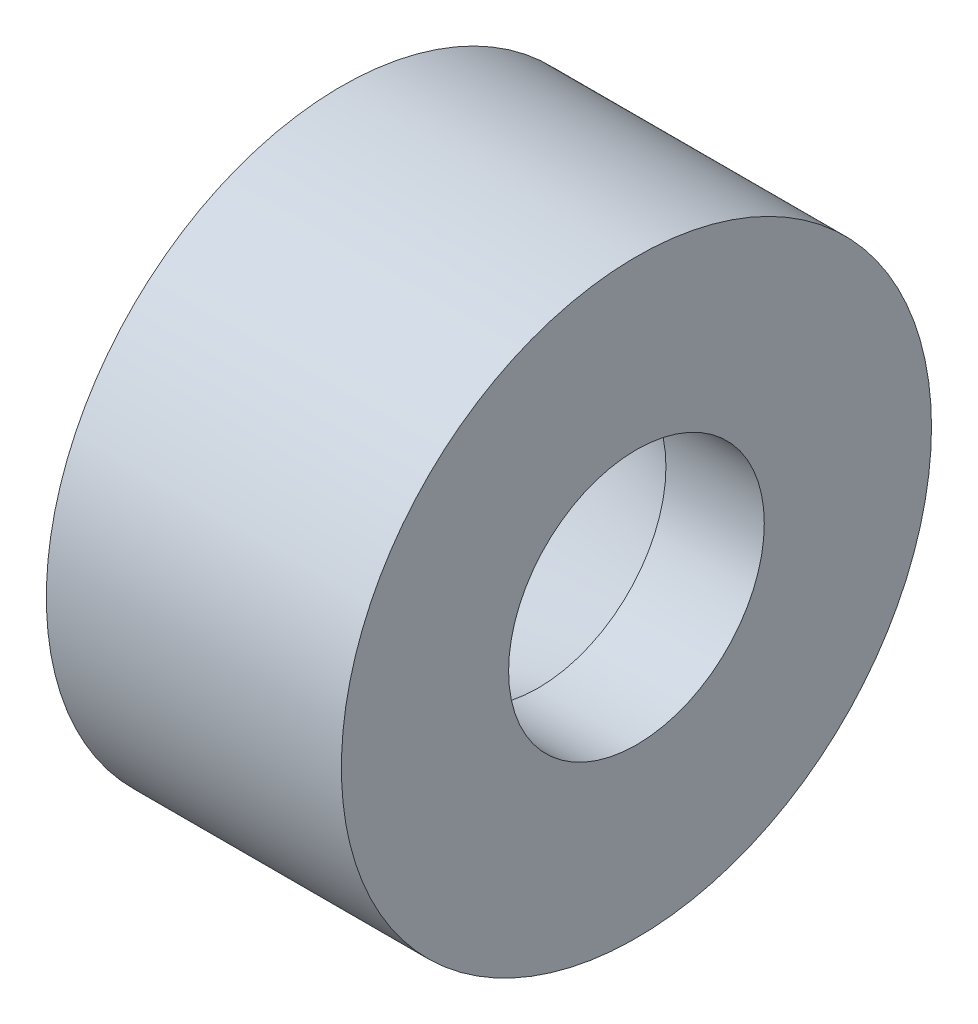
SolidWorks part; units mm, degrees
material "Ottone"
ref_plane "Piano frontale" through (0, 0, 0) normal (0, 0, 1) x (1, 0, 0)
ref_plane "Piano superiore" through (0, 0, 0) normal (0, 1, 0) x (1, 0, 0)
ref_plane "Piano destro" through (0, 0, 0) normal (1, 0, 0) x (0, 0, -1)
sketch "Schizzo1" plane through (0, 0, 0) normal (0, 0, 1) x (1, 0, 0)
  line L0 (0, 6.5) -> (-5, 6.5)
  line L1 (-5, 6.5) -> (-15, 10.1397)
  line L2 (-15, 10.1397) -> (-15, 15)
  line L3 (-15, 15) -> (0, 15)
  line L4 (0, 15) -> (0, 6.5)
  line L5 (0, 0) -> (-72.0223, 0) construction
  dimension "D1" = 20
  dimension "D2" = 10
  dimension "D3" = 15
  dimension "D4" = 13
  dimension "D5" = 30
revolve "Rivoluzione1" add sketch "Schizzo1" angle 360 about L5
